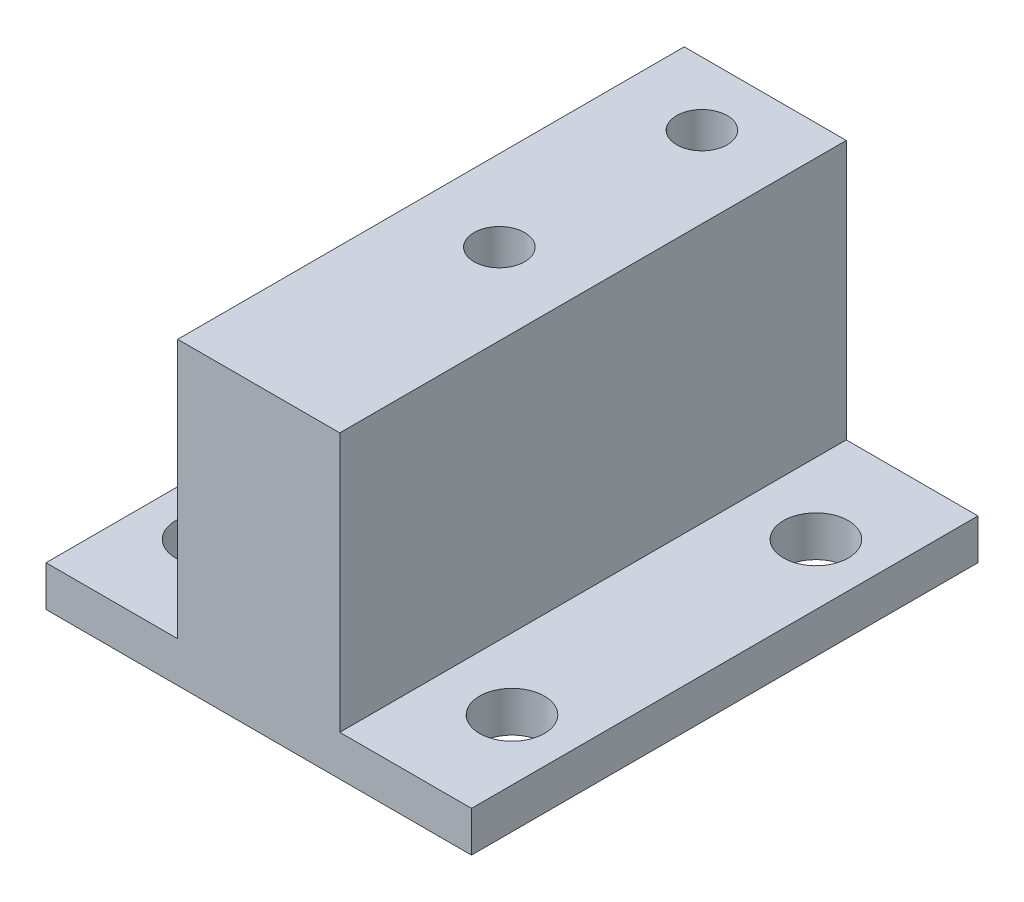
SolidWorks part; units mm, degrees
ref_plane "Front Plane" through (0, 0, 0) normal (0, 0, 1) x (1, 0, 0)
ref_plane "Top Plane" through (0, 0, 0) normal (0, 1, 0) x (1, 0, 0)
ref_plane "Right Plane" through (0, 0, 0) normal (1, 0, 0) x (0, 0, -1)
sketch "Sketch1" plane through (0, 0, 0) normal (0, 1, 0) x (1, 0, 0)
  line L1 (0, 0) -> (25, 0)
  line L2 (0, 0) -> (0, -25)
  line L3 (0, -25) -> (25, -25)
  line L4 (25, 0) -> (25, -25)
  dimension "D1" = 25
  dimension "D2" = 25
extrude "Boss-Extrude1" add sketch "Sketch1" along normal blind 14.8
sketch "Sketch2" plane through (0, 14.8, 0) normal (0, 1, 0) x (1, 0, 0)
  line L0 (0, -25) -> (25, -25) construction
  line L1 (25, -25) -> (25, 0) construction
  circle A0 centre (5, -20) radius 0.9466
  circle A1 centre (20, -20) radius 0.9466
  circle A2 centre (20, -5) radius 0.9466
  circle A3 centre (5, -5) radius 0.9466
  dimension "D3" = 5
  dimension "D4" = 1.8932
  dimension "D5" = 5
  dimension "D1" = 2
  dimension "D2" = 2
hole_wizard "M3 Clearance Hole1" positions "3DSketch1" profile "Sketch3" hole size "M3" standard "ANSI Metric" end condition through all
sketch3d "3DSketch1"
  point P0 (5, 14.8, 5)
  point P3 (20, 14.8, 5)
  point P6 (20, 14.8, 20)
  point P9 (5, 14.8, 20)
sketch "Sketch3" plane through (5, 14.8, 5) normal (1, 0, 0) x (0, 0, 1)
  line L0 (0, 0) -> (0, 14.8)
  line L1 (0, 14.8) -> (1.6, 14.8)
  line L2 (1.6, 14.8) -> (1.6, 0)
  line L5 (1.6, 0) -> (0, 0)
  line L11 (0, -6.35) -> (0, 107.95) construction
  dimension "Thru Hole Dia." = 3.2
  dimension "Thru Hole Depth" = 14.8
sketch "Sketch5" plane through (0, 14.8, 0) normal (0, 1, 0) x (1, 0, 0)
  circle A0 centre (12.5, -3.1242) radius 0.6151
  circle A1 centre (12.5, -13.1242) radius 0.6151
  dimension "D2" = 10
  dimension "D1" = 2
hole_wizard "M3x0.5 Tapped Hole2" positions "3DSketch2" profile "Sketch6" tap size "M3x0.5" standard "ANSI Metric"
sketch3d "3DSketch2"
  point P0 (12.5, 14.8, 3.1242)
  point P3 (12.5, 14.8, 13.1242)
cosmetic thread "Hole Thread1" parameters "D1"=6, "D2"=3
cosmetic thread "Hole Thread2" parameters "D1"=6, "D2"=3
sketch "Sketch6" plane through (12.5, 14.8, 3.1242) normal (1, 0, 0) x (0, 0, 1)
  line L0 (0, 0) -> (0, 8.2511)
  line L1 (0, 8.2511) -> (1.25, 7.5)
  line L2 (1.25, 7.5) -> (1.25, 0)
  line L5 (1.25, 0) -> (0, 0)
  line L10 (0, 8.2511) -> (-1.25, 7.5) construction
  line L11 (0, -6.35) -> (0, 107.95) construction
  dimension "Tap Drill Dia." = 2.5
  dimension "Tap Drill Depth" = 7.5
  dimension "Drill Angle" = 118
sketch "Sketch8" plane through (0, 14.8, 0) normal (0, 1, 0) x (1, 0, 0)
  line L0 (25, 0) -> (0, 0) construction
  line L1 (0, -25) -> (8.5, -25)
  line L2 (0, -25) -> (0, 0)
  line L3 (0, 0) -> (8.5, 0)
  line L4 (8.5, -25) -> (8.5, 0)
  dimension "D1" = 8.5
extrude "Cut-Extrude1" cut sketch "Sketch8" against normal blind 9.77
sketch "Sketch9" plane through (0, 14.8, 0) normal (0, 1, 0) x (1, 0, 0)
  line L0 (25, 0) -> (8.5, 0) construction
  line L1 (25, -25) -> (16.5, -25)
  line L2 (25, -25) -> (25, 0)
  line L3 (25, 0) -> (16.5, 0)
  line L4 (16.5, -25) -> (16.5, 0)
  dimension "D1" = 8.5
extrude "Cut-Extrude2" cut sketch "Sketch9" against normal blind 9.77
sketch "Sketch10" plane through (0, 5.03, 0) normal (0, 1, 0) x (1, 0, 0)
  line L0 (8.5, 0) -> (0, 0) construction
  line L1 (0, -25) -> (2, -25)
  line L2 (0, -25) -> (0, 0)
  line L3 (0, 0) -> (2, 0)
  line L4 (2, -25) -> (2, 0)
  dimension "D1" = 2
extrude "Cut-Extrude3" cut sketch "Sketch10" against normal blind 9.77
sketch "Sketch11" plane through (0, 5.03, 0) normal (0, 1, 0) x (1, 0, 0)
  line L0 (25, 0) -> (16.5, 0) construction
  line L1 (25, -25) -> (23, -25)
  line L2 (25, -25) -> (25, 0)
  line L3 (25, 0) -> (23, 0)
  line L4 (23, -25) -> (23, 0)
  dimension "D1" = 2
extrude "Cut-Extrude4" cut sketch "Sketch11" against normal blind 9.77
sketch "Sketch12" [suppressed] plane through (0, 12.8, 0) normal (0, 1, 0) x (1, 0, 0)
  line L0 (8.5, -25) -> (8.5, 0) construction
  circle A0 centre (10.5, -8.1242) radius 0.6619
  circle A1 centre (14.5, -8.1242) radius 0.6619
  circle A2 centre (12.5, -13.1242) radius 1.25 construction
  dimension "D2" = 2
  dimension "D3" = 5
  dimension "D1" = 2
hole_wizard "Ø2.0mm Dowel Hole1" [suppressed] positions "3DSketch3" profile "Sketch13" hole size "Ø2.0" standard "ANSI Metric"
sketch3d "3DSketch3" [suppressed]
  point P0 (14.5, 12.8, 8.1242)
  point P3 (10.5, 12.8, 8.1242)
sketch "Sketch13" plane through (14.5, 12.8, 8.1242) normal (1, 0, 0) x (0, 0, 1)
  line L0 (0, 0) -> (0, 5.6009)
  line L1 (0, 5.6009) -> (1, 5)
  line L2 (1, 5) -> (1, 0)
  line L5 (1, 0) -> (0, 0)
  line L10 (0, 5.6009) -> (-1, 5) construction
  line L11 (0, -6.35) -> (0, 107.95) construction
  dimension "Hole Dia." = 2
  dimension "Hole Depth" = 5
  dimension "Drill Angle" = 118
sketch "Sketch16" plane through (0, 5.03, 0) normal (0, 1, 0) x (1, 0, 0)
  line L1 (8.5, -25) -> (2, -25)
  line L2 (8.5, -25) -> (8.5, 0)
  line L3 (8.5, 0) -> (2, 0)
  line L4 (2, -25) -> (2, 0)
extrude "Cut-Extrude6" cut sketch "Sketch16" against normal blind 3.03
sketch "Sketch17" plane through (0, 5.03, 0) normal (0, 1, 0) x (1, 0, 0)
  line L1 (23, -25) -> (16.5, -25)
  line L2 (23, -25) -> (23, 0)
  line L3 (23, 0) -> (16.5, 0)
  line L4 (16.5, -25) -> (16.5, 0)
extrude "Cut-Extrude7" cut sketch "Sketch17" against normal blind 3.03
